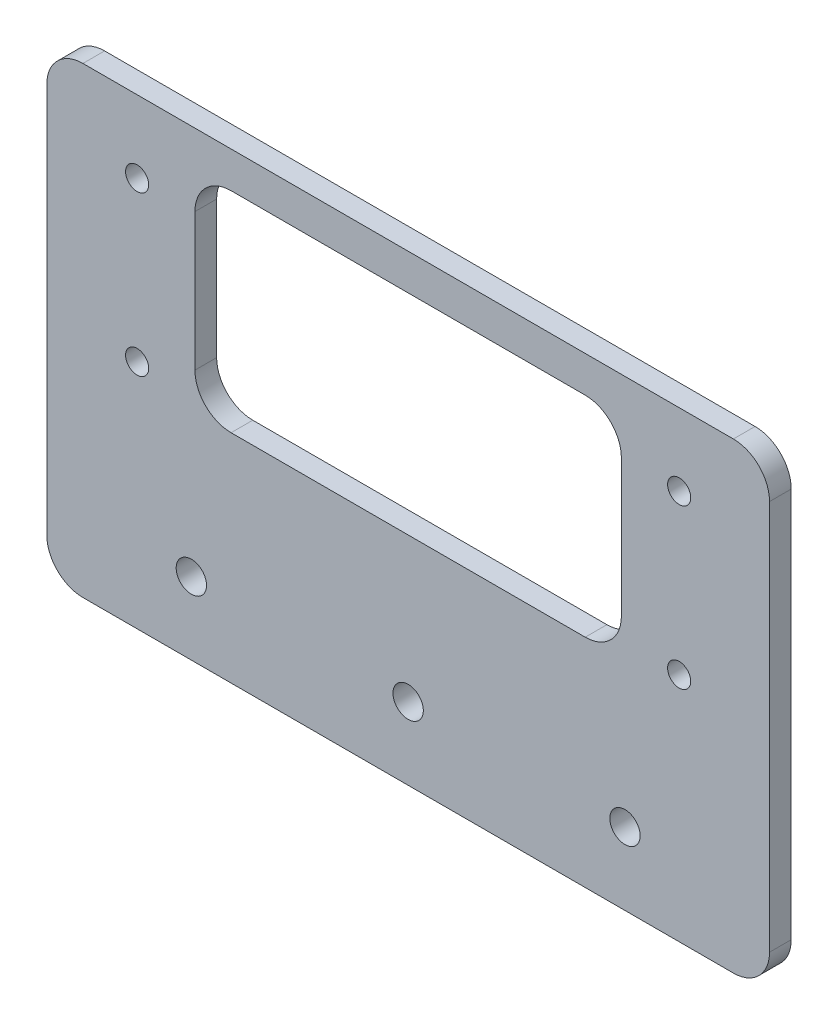
SolidWorks part; units mm, degrees
material "A-玻璃纤维"
ref_plane "前视基准面" through (0, 0, 0) normal (0, 0, 1) x (1, 0, 0)
ref_plane "上视基准面" through (0, 0, 0) normal (0, 1, 0) x (1, 0, 0)
ref_plane "右视基准面" through (0, 0, 0) normal (1, 0, 0) x (0, 0, -1)
sketch "草图1" plane through (0, 0, 0) normal (0, 0, 1) x (1, 0, 0)
  line L0 (0, 74.5554) -> (0, -82.2531) construction
  line L1 (-50, -32) -> (50, -32)
  line L2 (-50, -32) -> (-50, 32)
  line L3 (-50, 32) -> (50, 32)
  line L4 (50, -32) -> (50, 32)
  line L5 (-50, -32) -> (50, 32) construction
  line L6 (-50, 32) -> (50, -32) construction
  circle A0 centre (-37.5, 0) radius 1.6
  circle A1 centre (-37.5, 22) radius 1.6
  circle A2 centre (37.5, 0) radius 1.6
  circle A3 centre (37.5, 22) radius 1.6
  circle A4 centre (-30, -22) radius 2.1
  circle A5 centre (30, -22) radius 2.1
  circle A6 centre (0, -22) radius 2.1
  point P0 (0, 0)
  dimension "D1" = 22
  dimension "D2" = 75
  dimension "D3" = 3.2
  dimension "D4" = 10
  dimension "D5" = 30
  dimension "D6" = 10
  dimension "D7" = 22
  dimension "D10" = 4.2
  dimension "D8" = 64
  dimension "D9" = 100
extrude "凸台-拉伸1" add sketch "草图1" along normal blind 3
sketch "草图2" plane through (0, 0, 3) normal (0, 0, 1) x (1, 0, 0)
  line L0 (50, 32) -> (-50, 32) construction
  line L1 (-29.5, 27) -> (29.5, 27)
  line L2 (-29.5, 27) -> (-29.5, -2)
  line L3 (-29.5, -2) -> (29.5, -2)
  line L4 (29.5, 27) -> (29.5, -2)
  line L5 (-29.5, 27) -> (29.5, -2) construction
  line L6 (-29.5, -2) -> (29.5, 27) construction
  circle A0 centre (37.5, 22) radius 1.6 construction
  circle A1 centre (-37.5, 0) radius 1.6 construction
  circle A2 centre (-30, -22) radius 2.1 construction
  point P0 (0, 12.5)
  dimension "D1" = 5
  dimension "D2" = 8
  dimension "D3" = 8
  dimension "D4" = 20
extrude "切除-拉伸1" cut sketch "草图2" against normal blind 10
fillet "圆角1" radius 5 4 edges at (29.5, -2, 1.5) (-29.5, -2, 1.5) (-29.5, 27, 1.5) (29.5, 27, 1.5)
fillet "圆角2" radius 5 4 edges at (50, -32, 1.5) (-50, -32, 1.5) (-50, 32, 1.5) (50, 32, 1.5)
